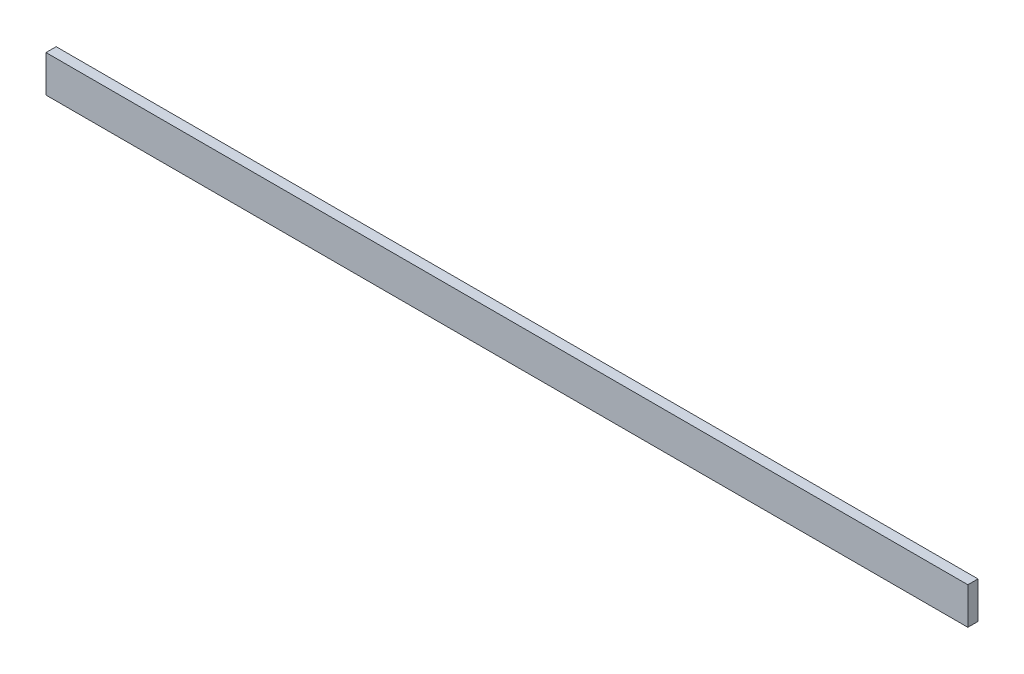
SolidWorks part; units mm, degrees
ref_plane "Plan de face" through (0, 0, 0) normal (0, 0, 1) x (1, 0, 0)
ref_plane "Plan de dessus" through (0, 0, 0) normal (0, 1, 0) x (1, 0, 0)
ref_plane "Plan de droite" through (0, 0, 0) normal (1, 0, 0) x (0, 0, -1)
sketch "Esquisse1" plane through (0, 0, 0) normal (0, 0, 1) x (1, 0, 0)
  line L1 (0, 0) -> (2000, 0)
  line L2 (0, 0) -> (0, 80)
  line L3 (0, 80) -> (2000, 80)
  line L4 (2000, 0) -> (2000, 80)
  dimension "D1" = 2000
  dimension "D2" = 80
extrude "Extrusion1" add sketch "Esquisse1" along normal blind 22
